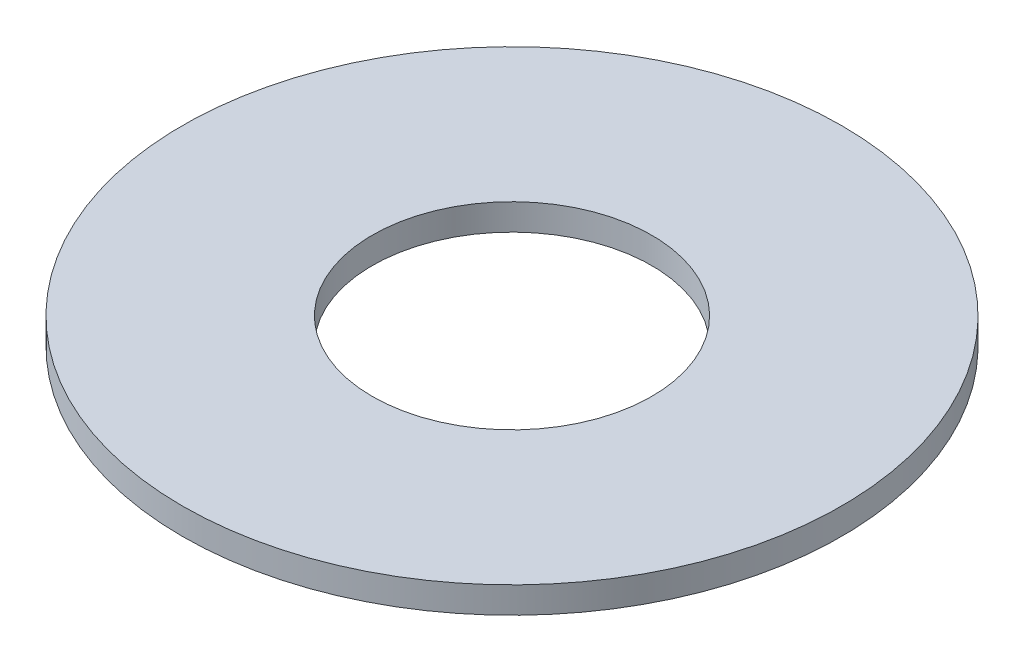
SolidWorks part; units mm, degrees
ref_plane "Front Plane" through (0, 0, 0) normal (0, 0, 1) x (1, 0, 0)
ref_plane "Top Plane" through (0, 0, 0) normal (0, 1, 0) x (1, 0, 0)
ref_plane "Right Plane" through (0, 0, 0) normal (1, 0, 0) x (0, 0, -1)
sketch "Sketch2" plane through (0, 0, 0) normal (0, 1, 0) x (1, 0, 0)
  circle A0 centre (0, 0) radius 12.5
  circle A1 centre (0, 0) radius 5.3
  dimension "D1" = 10.6
  dimension "D2" = 25
extrude "Boss-Extrude1" add sketch "Sketch2" along normal mid plane 1
